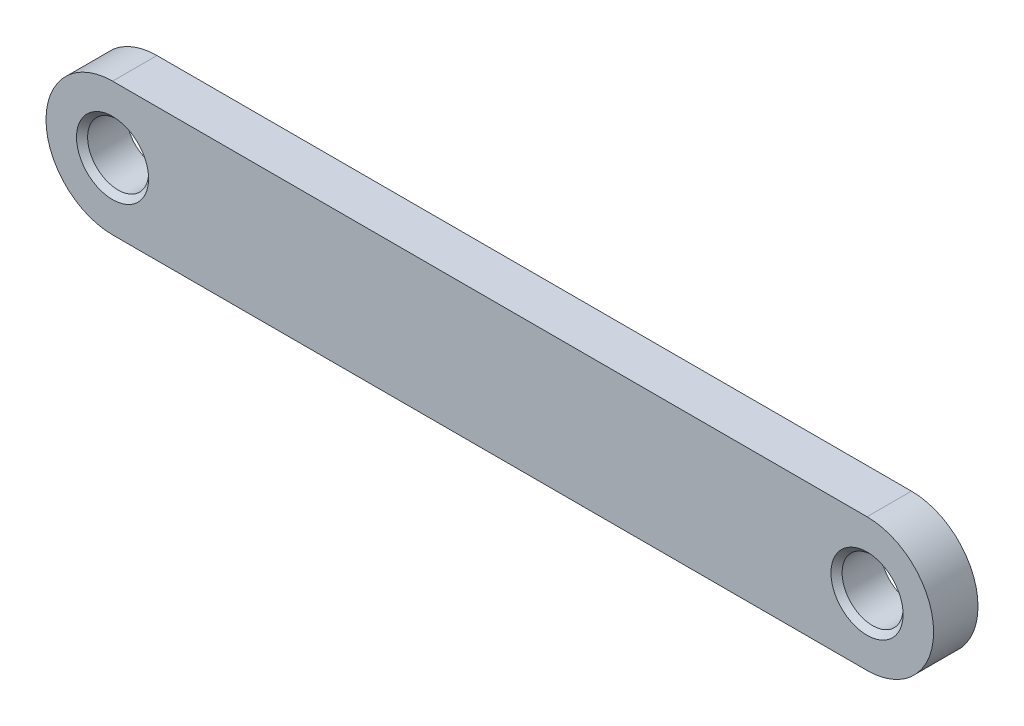
SolidWorks part; units mm, degrees
ref_plane "Front Plane" through (0, 0, 0) normal (0, 0, 1) x (1, 0, 0)
ref_plane "Top Plane" through (0, 0, 0) normal (0, 1, 0) x (1, 0, 0)
ref_plane "Right Plane" through (0, 0, 0) normal (1, 0, 0) x (0, 0, -1)
sketch "Sketch1" plane through (0, 0, 0) normal (0, 0, 1) x (1, 0, 0)
  line L0 (44.5, -47.65) -> (10.5, -47.65)
  line L1 (44.5, -53.65) -> (10.5, -53.65)
  arc A0 (44.5, -47.65) -> (44.5, -53.65) centre (44.5, -50.65) cw
  arc A1 (10.5, -47.65) -> (10.5, -53.65) centre (10.5, -50.65) ccw
  circle A2 centre (10.5, -50.65) radius 1.375
  circle A3 centre (44.5, -50.65) radius 1.375
  circle A5 centre (10.5, -50.65) radius 1.375 construction
extrude "Boss-Extrude1" add sketch "Sketch1" along normal blind 2
chamfer "Chamfer1" distance 0.25 angle 45 2 edges at (45.875, -50.65, 2) (11.875, -50.65, 2)
